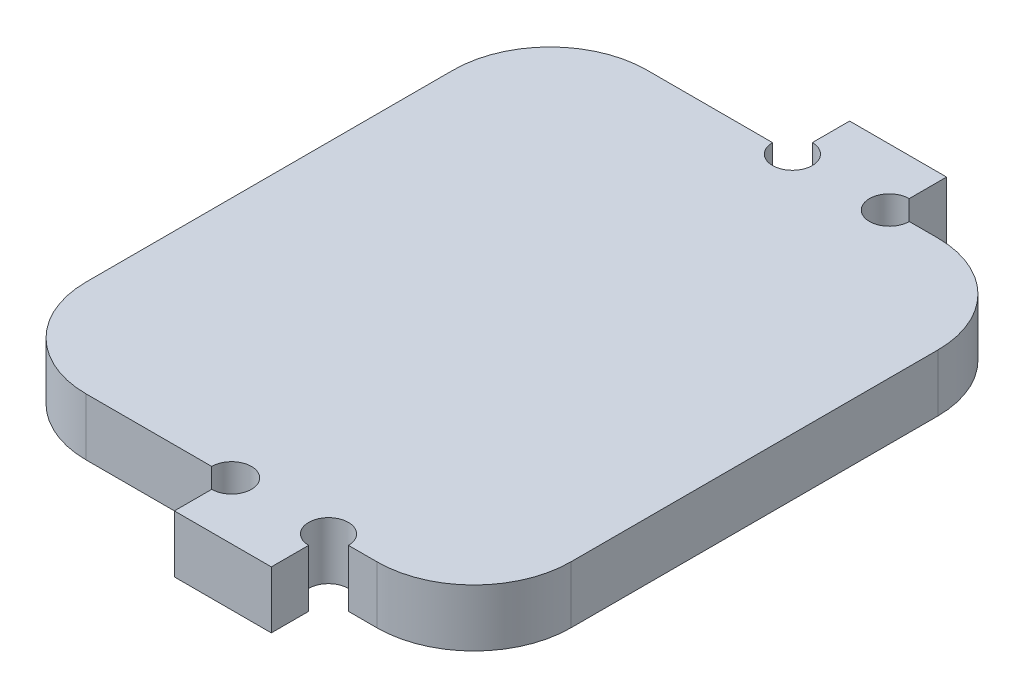
SolidWorks part; units mm, degrees
ref_plane "Front Plane" through (0, 0, 0) normal (0, 0, 1) x (1, 0, 0)
ref_plane "Top Plane" through (0, 0, 0) normal (0, 1, 0) x (1, 0, 0)
ref_plane "Right Plane" through (0, 0, 0) normal (1, 0, 0) x (0, 0, -1)
sketch "Sketch1" plane through (0, 0, 0) normal (0, 1, 0) x (1, 0, 0)
  line L1 (-25, -28.925) -> (25, -28.925)
  line L2 (-25, -28.925) -> (-25, 28.925)
  line L3 (-25, 28.925) -> (25, 28.925)
  line L4 (25, -28.925) -> (25, 28.925)
  line L5 (-25, -28.925) -> (25, 28.925) construction
  line L6 (-25, 28.925) -> (25, -28.925) construction
  line L7 (0, 23.025) -> (10, 23.025)
  line L8 (0, 23.025) -> (0, 34.825)
  line L9 (0, 34.825) -> (10, 34.825)
  line L10 (10, 23.025) -> (10, 34.825)
  line L11 (0, 23.025) -> (10, 34.825) construction
  line L12 (0, 34.825) -> (10, 23.025) construction
  line L13 (0, -34.825) -> (10, -34.825)
  line L14 (0, -34.825) -> (0, -23.025)
  line L15 (0, -23.025) -> (10, -23.025)
  line L16 (10, -34.825) -> (10, -23.025)
  line L17 (0, -34.825) -> (10, -23.025) construction
  line L18 (0, -23.025) -> (10, -34.825) construction
  point P0 (0, 0)
  point P5 (5, 28.925)
  point P11 (5, -28.925)
  dimension "D1" = 57.85
  dimension "D2" = 50
  dimension "D3" = 11.8
  dimension "D4" = 10
  dimension "D6" = 10
  dimension "D7" = 20
extrude "Boss-Extrude1" add sketch "Sketch1" along normal blind 5.9 contours L16 L1 L4 L3 L10 L7 L8 L2 L14 L15 | L1 L16 L15 L14 | L13 L16 L1 L14 | L7 L10 L3 L8 | L3 L10 L9 L8
fillet "Fillet1" radius 10 4 edges at (25, 2.95, -28.925) (25, 2.95, 28.925) (-25, 2.95, 28.925) (-25, 2.95, -28.925)
sketch "Sketch2" plane through (0, 5.9, 0) normal (0, 1, 0) x (1, 0, 0)
  circle A0 centre (0, 28.925) radius 2.05
  circle A1 centre (10, 28.925) radius 2.05
  circle A2 centre (0, -28.925) radius 2.05
  circle A3 centre (10, -28.925) radius 2.05
  dimension "D1" = 4.1
extrude "Cut-Extrude1" cut sketch "Sketch2" against normal up to next
equation "\"e\" = 5.9"
equation "\"D1@Boss-Extrude1\"=\"e\""
equation "\"D3@Sketch1\"= 2 * \"e\""
